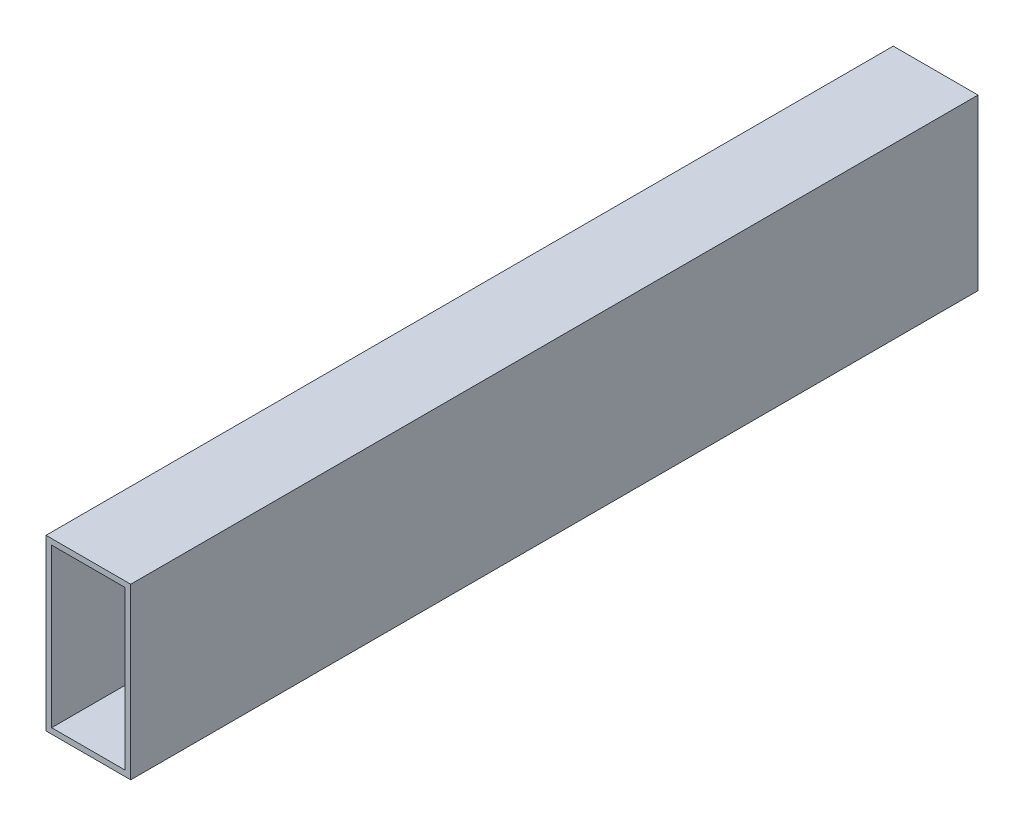
SolidWorks part; units mm, degrees
ref_plane "Front Plane" through (0, 0, 0) normal (0, 0, 1) x (1, 0, 0)
ref_plane "Top Plane" through (0, 0, 0) normal (0, 1, 0) x (1, 0, 0)
ref_plane "Right Plane" through (0, 0, 0) normal (1, 0, 0) x (0, 0, -1)
curve "Curve1"
  spline degree 1 poles (0, 0, -300) (0, 0, 300) knots 0 0 1 1
sketch "Sketch1" plane through (0, 0, 0) normal (0, 0, 1) x (1, 0, 0)
  line L0 (0, 35.3535) -> (0, -33.8384) construction
  line L1 (-30, 60) -> (30, 60)
  line L2 (-30, 60) -> (-30, -60)
  line L3 (-30, -60) -> (30, -60)
  line L4 (30, 60) -> (30, -60)
  line L5 (-26, 56) -> (26, 56)
  line L6 (-26, 56) -> (-26, -56)
  line L7 (-26, -56) -> (26, -56)
  line L8 (26, 56) -> (26, -56)
  line L9 (-39.3939, 0) -> (41.5152, 0) construction
  dimension "D1" = 60
  dimension "D2" = 52
  dimension "D3" = 120
  dimension "D4" = 112
sweep "Sweep1" add profiles "Sketch1" path "Curve1"
